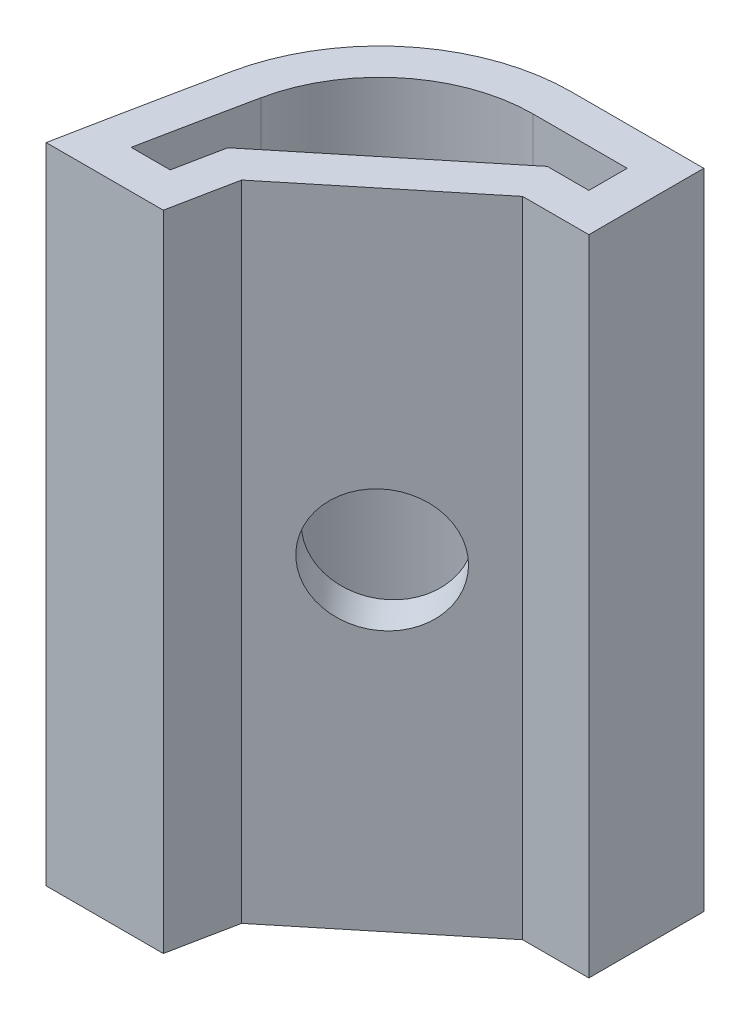
SolidWorks part; units mm, degrees
ref_plane "Front Plane" through (0, 0, 0) normal (0, 0, 1) x (1, 0, 0)
ref_plane "Top Plane" through (0, 0, 0) normal (0, 1, 0) x (1, 0, 0)
ref_plane "Right Plane" through (0, 0, 0) normal (1, 0, 0) x (0, 0, -1)
sketch "Sketch1" plane through (0, 0, 0) normal (0, 1, 0) x (1, 0, 0)
  line L12 (-4.6271, -3.9731) -> (-1.5699, -3.9731)
  line L13 (2.8067, 1.0269) -> (4.5352, 1.0269)
  line L14 (4.5352, 1.0269) -> (4.5352, 4.0269)
  line L17 (4.5352, 4.0269) -> (1.0781, 4.0269)
  line L18 (-1.2293, -2.2687) -> (2.8067, 1.0269)
  line L21 (-3.4106, -2.9731) -> (-2.3909, -2.9731)
  line L22 (3.5352, 3.0269) -> (1.0781, 3.0269)
  line L23 (3.5352, 2.0269) -> (3.5352, 3.0269)
  line L24 (2.4503, 2.0269) -> (3.5352, 2.0269)
  line L25 (-2.1383, -1.7199) -> (2.4503, 2.0269)
  arc A8 (-3.8173, 0.0443) -> (-4.6271, -3.9731) centre (330.6759, -69.4731) ccw
  arc A9 (-1.2293, -2.2687) -> (-1.5699, -3.9731) centre (330.6759, -69.4731) ccw
  arc A12 (1.0781, 4.0269) -> (-3.8173, 0.0443) centre (1.0781, -0.9731) ccw
  arc A13 (-2.1383, -1.7199) -> (-2.3909, -2.9731) centre (330.6759, -69.4731) ccw
  arc A17 (-2.8382, -0.1591) -> (-3.4106, -2.9731) centre (330.6759, -69.4731) ccw
  arc A18 (1.0781, 3.0269) -> (-2.8382, -0.1591) centre (1.0781, -0.9731) ccw
  point P13 (0.5091, 4.5)
  point P14 (-4.8758, 0.1191)
  point P15 (330.1068, -69.5)
  point P16 (-5.8027, -4.5)
  point P23 (4.4662, 4.5)
  dimension "D1" = 1
extrude "Boss-Extrude1" add sketch "Sketch1" along normal blind 16.8
sketch "Sketch3" plane through (0.6197, 0, 0.7589) normal (0.6325, 0, 0.7746) x (0.7746, 0, -0.6325)
  line L0 (0.2182, 16.8) -> (0.2182, 0) construction
  line L1 (-2.3871, 16.8) -> (2.8235, 16.8) construction
  line L2 (-2.3871, 0) -> (2.8235, 0) construction
  line L4 (11.5458, 3.5498) -> (11.5052, 3.4685) construction
  circle A0 centre (0.2182, 8.4) radius 1.6022
  dimension "D1" = 3.2044
extrude "Cut-Extrude2" cut sketch "Sketch3" against normal up to surface (1 mm away) up to face at (0.156, 8.4, -0.1535)
